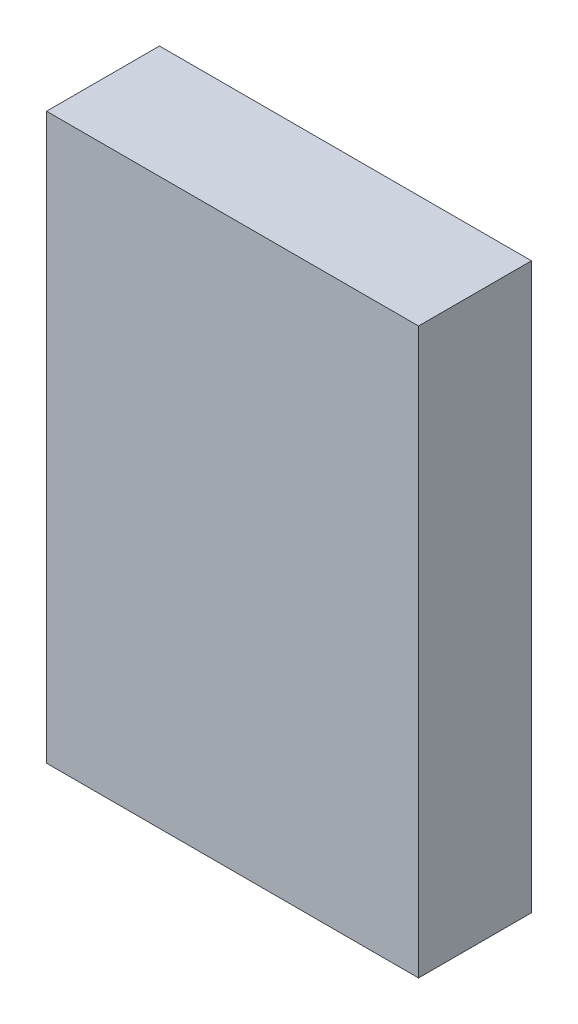
SolidWorks part; units mm, degrees
ref_plane "Front Plane" through (0, 0, 0) normal (0, 0, 1) x (1, 0, 0)
ref_plane "Top Plane" through (0, 0, 0) normal (0, 1, 0) x (1, 0, 0)
ref_plane "Right Plane" through (0, 0, 0) normal (1, 0, 0) x (0, 0, -1)
sketch "Sketch1" plane through (0, 0, 0) normal (0, 0, 1) x (1, 0, 0)
  line L1 (-28, -42.5) -> (28, -42.5)
  line L2 (-28, -42.5) -> (-28, 42.5)
  line L3 (-28, 42.5) -> (28, 42.5)
  line L4 (28, -42.5) -> (28, 42.5)
  line L5 (-28, -42.5) -> (28, 42.5) construction
  line L6 (-28, 42.5) -> (28, -42.5) construction
  point P0 (0, 0)
  dimension "D1" = 85
  dimension "D2" = 56
extrude "Boss-Extrude1" add sketch "Sketch1" along normal blind 17
